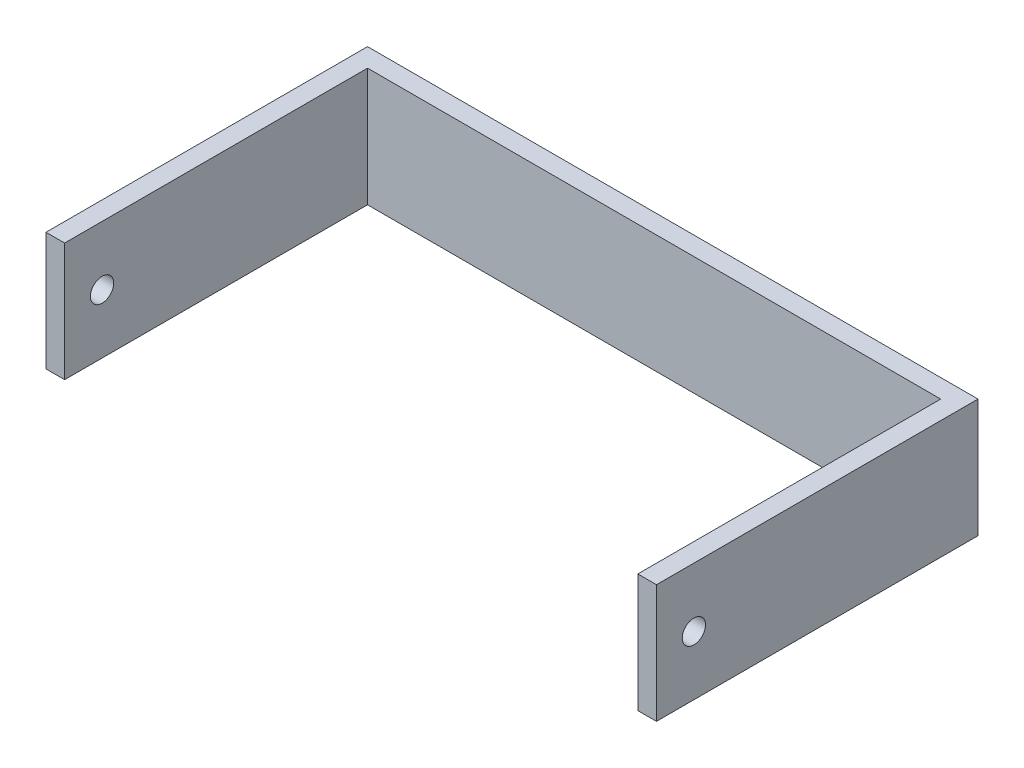
SolidWorks part; units mm, degrees
ref_plane "Alzado" through (0, 0, 0) normal (0, 0, 1) x (1, 0, 0)
ref_plane "Planta" through (0, 0, 0) normal (0, 1, 0) x (1, 0, 0)
ref_plane "Vista lateral" through (0, 0, 0) normal (1, 0, 0) x (0, 0, -1)
sketch "Croquis1" plane through (0, 0, 0) normal (0, 1, 0) x (1, 0, 0)
  line L0 (-71.7178, 0) -> (51.2822, 0)
  line L1 (51.2822, 0) -> (51.2822, -65)
  line L2 (-71.7178, 0) -> (-71.7178, -65)
  line L3 (-71.7178, -65) -> (-75.7178, -65)
  line L4 (-75.7178, -65) -> (-75.7178, 4)
  line L5 (51.2822, -65) -> (55.2822, -65)
  line L6 (55.2822, -65) -> (55.2822, 4)
  line L7 (-75.7178, 4) -> (55.2822, 4)
extrude "Saliente-Extruir1" add sketch "Croquis1" along normal blind 25.4
ref_plane "Plano1" through (55.2822, 0, 65) normal (0, -1, 0) x (-1, 0, 0)
sketch "Croquis3" plane through (55.2822, 0, 0) normal (1, 0, 0) x (0, 0, -1)
  circle A0 centre (-56.9692, 12.7) radius 2.5
  point P1 (0, 0)
extrude "Cortar-Extruir1" cut sketch "Croquis3" against normal through all both and the other way through all
